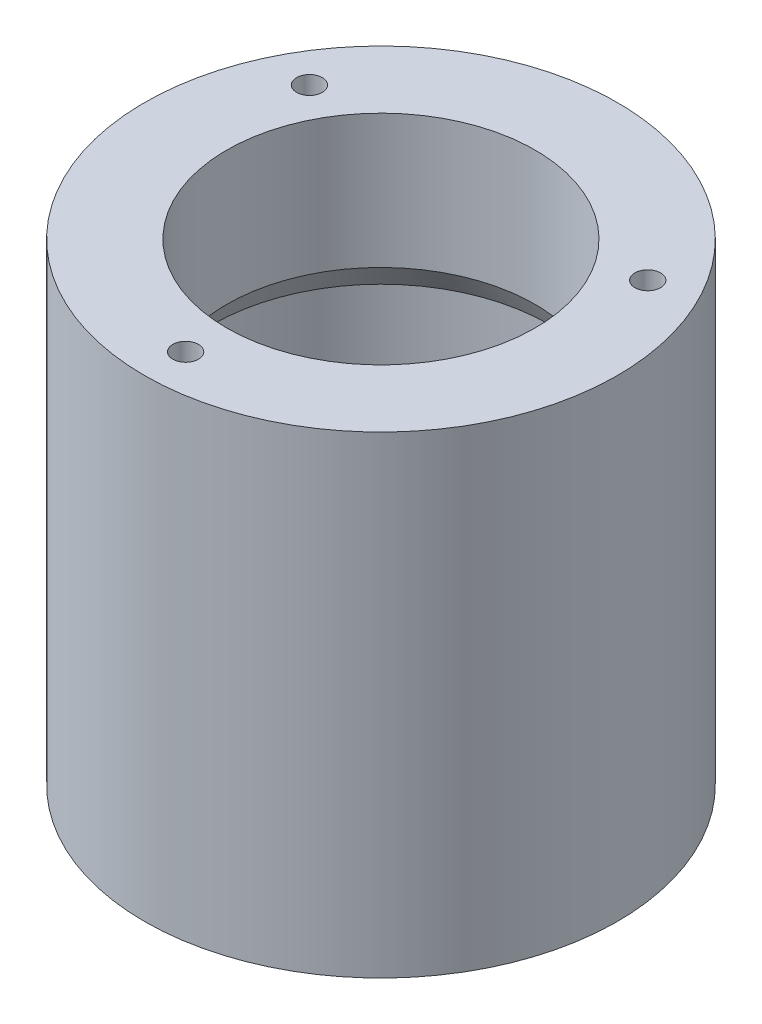
SolidWorks part; units mm, degrees
material "3.1325 (EN-AW 2017A)"
ref_plane "Plan de face" through (0, 0, 0) normal (0, 0, 1) x (1, 0, 0)
ref_plane "Plan de dessus" through (0, 0, 0) normal (0, 1, 0) x (1, 0, 0)
ref_plane "Plan de droite" through (0, 0, 0) normal (1, 0, 0) x (0, 0, -1)
sketch "Esquisse1" plane through (0, 0, 0) normal (0, 0, 1) x (1, 0, 0)
  line L0 (0, 0) -> (23, 0)
  line L1 (23, 0) -> (23, 46)
  line L2 (15, 46) -> (15, 33)
  line L3 (15, 6) -> (0, 6)
  line L4 (0, 6) -> (0, 0)
  line L5 (23, 46) -> (15, 46)
  line L8 (16.3771, 30.6148) -> (16.3771, 18.3852)
  line L9 (15, 16) -> (15, 6)
  line L10 (15, 33) -> (16.3771, 30.6148)
  line L11 (15, 16) -> (16.3771, 18.3852)
  dimension "D1" = 23
  dimension "D2" = 6
  dimension "D3" = 46
  dimension "D4" = 15
  dimension "D6" = 27
revolve "Révolution1" add sketch "Esquisse1" angle 360 about L4
sketch "Esquisse2" plane through (0, 0, 0) normal (0, -1, 0) x (1, 0, 0)
  circle A0 centre (0, 0) radius 12.5
extrude "Enlèv. mat.-Extru.1" cut sketch "Esquisse2" against normal through all
hole_wizard "Trou taraudé M51" positions "Esquisse4" profile "Esquisse3" tap size "M5" standard "ISO"
sketch "Esquisse4" plane through (0, 0, 0) normal (0, -1, 0) x (1, 0, 0)
  point P0 (0, 19)
  dimension "D1" = 0
  dimension "D2" = 19
sketch "Esquisse3" plane through (0, 0, 19) normal (1, 0, 0) x (0, 0, -1)
  line L0 (0, 0) -> (0, 13.2618)
  line L1 (0, 13.2618) -> (2.1, 12)
  line L2 (2.1, 12) -> (2.1, 0)
  line L5 (2.1, 0) -> (0, 0)
  line L10 (0, 13.2618) -> (-2.1, 12) construction
  line L11 (0, -6.35) -> (0, 107.95) construction
  dimension "Diamètre du trou pour taraudage" = 4.2
  dimension "Profondeur du trou pour taraudage" = 12
  dimension "Angle de pointe" = 118
cosmetic thread "Filetage de perçage1" parameters "D1"=10, "D2"=5
pattern_circular "Répétition circulaire1" count 3 over 360 about axis through (0, 0, 0) along (0, 1, 0) of "Trou taraudé M51"
hole_wizard "Trou taraudé M31" positions "Esquisse8" profile "Esquisse7" tap size "M3" standard "ISO"
sketch "Esquisse8" plane through (0, 46, 0) normal (0, 1, 0) x (-1, 0, 0)
  point P0 (0, 19)
  dimension "D1" = 0
  dimension "D2" = 19
sketch "Esquisse7" plane through (0, 46, 19) normal (1, 0, 0) x (0, 0, 1)
  line L0 (0, 0) -> (0, 9.2511)
  line L1 (0, 9.2511) -> (1.25, 8.5)
  line L2 (1.25, 8.5) -> (1.25, 0)
  line L5 (1.25, 0) -> (0, 0)
  line L10 (0, 9.2511) -> (-1.25, 8.5) construction
  line L11 (0, -6.35) -> (0, 107.95) construction
  dimension "Diamètre du trou pour taraudage" = 2.5
  dimension "Profondeur du trou pour taraudage" = 8.5
  dimension "Angle de pointe" = 118
cosmetic thread "Filetage de perçage2" parameters "D1"=6, "D2"=3
pattern_circular "Répétition circulaire2" count 3 over 360 about axis through (0, 0, 0) along (0, 1, 0) of "Trou taraudé M31"
